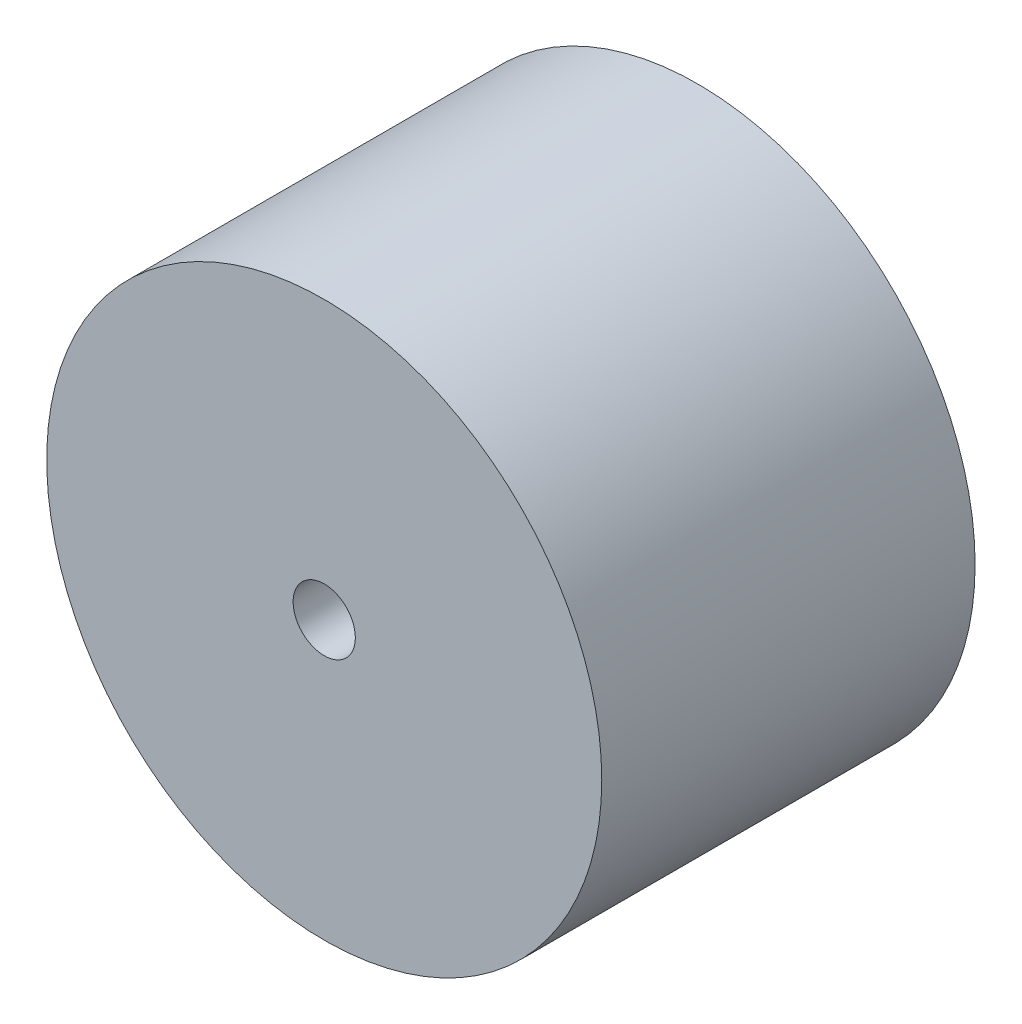
SolidWorks part; units mm, degrees
material "6061-T6 (SS)"
ref_plane "Front Plane" through (0, 0, 0) normal (0, 0, 1) x (1, 0, 0)
ref_plane "Top Plane" through (0, 0, 0) normal (0, 1, 0) x (1, 0, 0)
ref_plane "Right Plane" through (0, 0, 0) normal (1, 0, 0) x (0, 0, -1)
sketch "Sketch2" plane through (0, 0, 0) normal (0, 0, 1) x (1, 0, 0)
  circle A0 centre (0, 0) radius 28.321
  circle A1 centre (0, 0) radius 3.175
  dimension "D1" = 56.642
  dimension "D2" = 6.35
extrude "Boss-Extrude1" add sketch "Sketch2" along normal blind 38.1
equation "\"Thick\"= \"in\""
